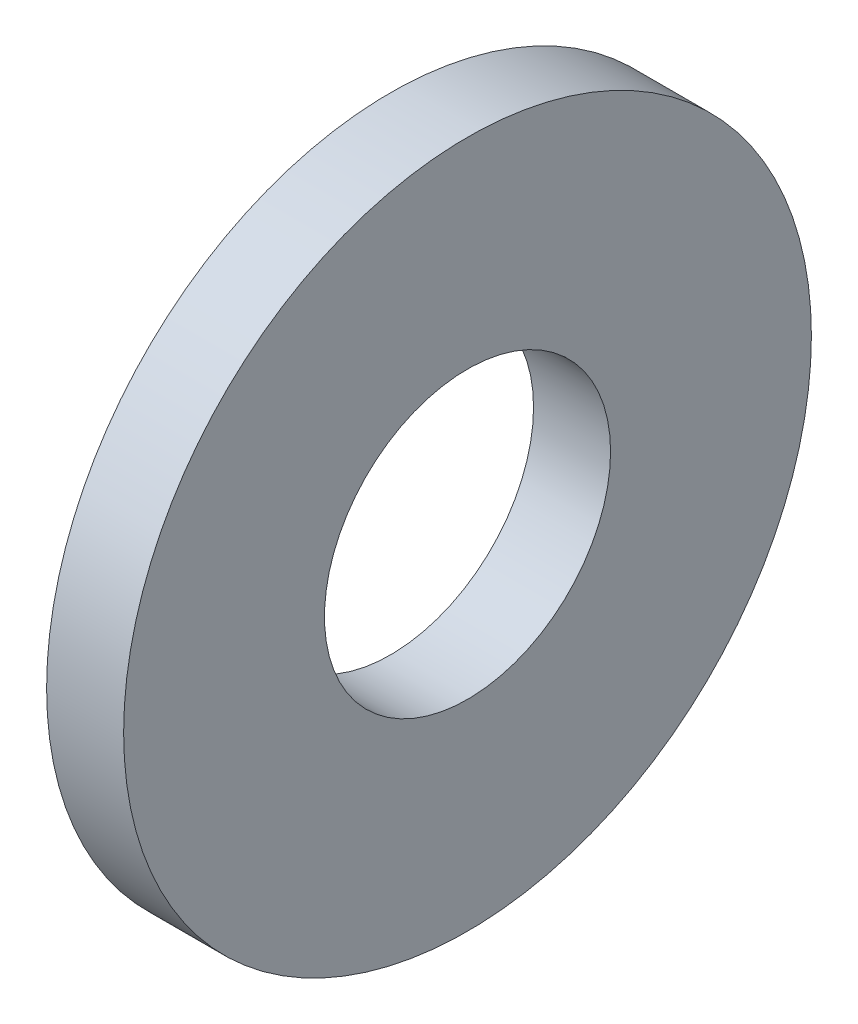
SolidWorks part; units mm, degrees
ref_plane "Front Plane" through (0, 0, 0) normal (0, 0, 1) x (1, 0, 0)
ref_plane "Top Plane" through (0, 0, 0) normal (0, 1, 0) x (1, 0, 0)
ref_plane "Right Plane" through (0, 0, 0) normal (1, 0, 0) x (0, 0, -1)
sketch "Sketch1" plane through (0, 0, 0) normal (1, 0, 0) x (0, 0, -1)
  circle A0 centre (0, 0) radius 7.9375
  circle A1 centre (0, 0) radius 3.302
  dimension "OD" = 15.875
  dimension "ID" = 6.604
extrude "Boss-Extrude1" add sketch "Sketch1" along normal blind 1.778
